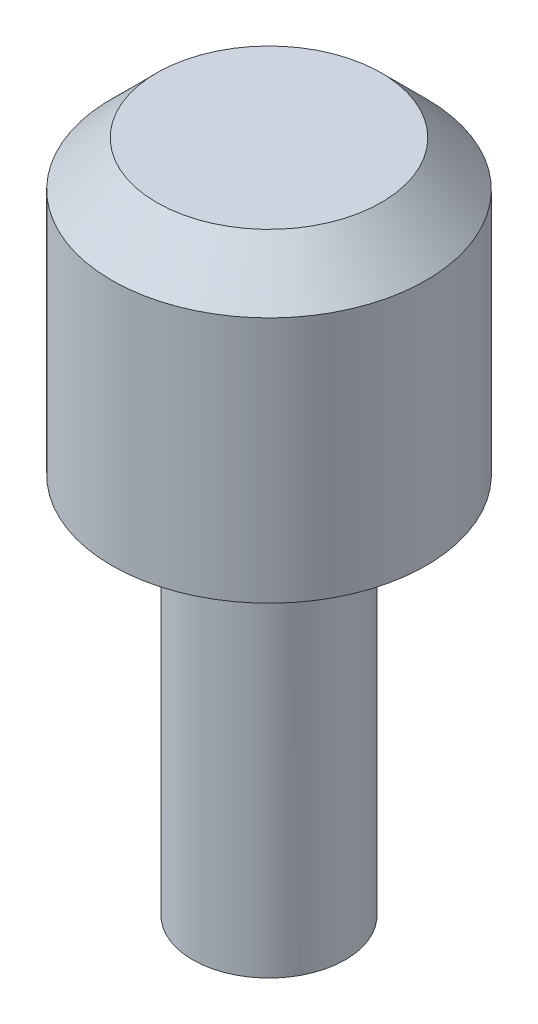
SolidWorks part; units mm, degrees
material "Delrin 2700 NC010, Low Viscosity Acetal Copolymer (SS)"
ref_plane "Front Plane" through (0, 0, 0) normal (0, 0, 1) x (1, 0, 0)
ref_plane "Top Plane" through (0, 0, 0) normal (0, 1, 0) x (1, 0, 0)
ref_plane "Right Plane" through (0, 0, 0) normal (1, 0, 0) x (0, 0, -1)
sketch "Sketch1" plane through (0, 0, 0) normal (0, 1, 0) x (1, 0, 0)
  circle A0 centre (0, 0) radius 3.5
  dimension "D1" = 7
extrude "Boss-Extrude1" add sketch "Sketch1" along normal blind 6.5
chamfer "Chamfer1" distance 1 angle 45 1 edges at (0, 6.5, 3.5)
sketch "Sketch2" plane through (0, 0, 0) normal (0, -1, 0) x (1, 0, 0)
  circle A0 centre (0, 0) radius 1.7
  dimension "D1" = 3.4
extrude "Boss-Extrude2" add sketch "Sketch2" along normal blind 8.5
